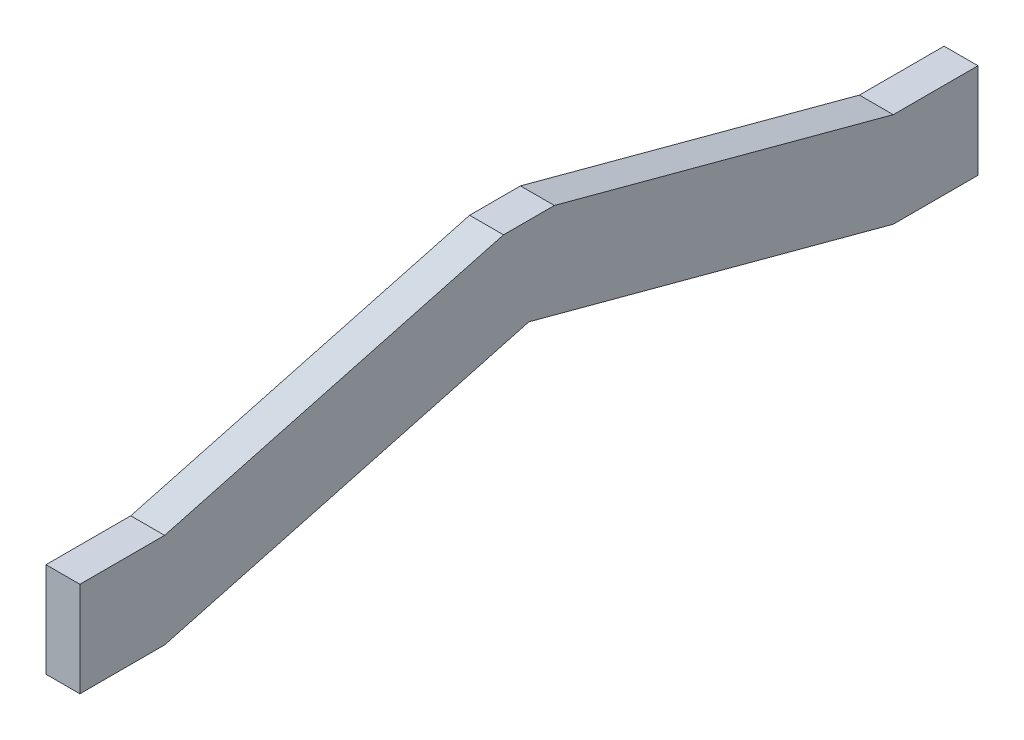
SolidWorks part; units mm, degrees
ref_plane "Front Plane" through (0, 0, 0) normal (0, 0, 1) x (1, 0, 0)
ref_plane "Top Plane" through (0, 0, 0) normal (0, 1, 0) x (1, 0, 0)
ref_plane "Right Plane" through (0, 0, 0) normal (1, 0, 0) x (0, 0, -1)
sketch "Sketch1" plane through (0, 0, 0) normal (1, 0, 0) x (0, 0, -1)
  line L10 (0, 0) -> (-25, 0)
  line L11 (-25, 0) -> (-132.5, 28.8045)
  line L12 (-132.5, 28.8045) -> (-240, 0)
  line L13 (-240, 0) -> (-265, 0)
  line L14 (-265, 0) -> (-265, 28)
  line L15 (-265, 28) -> (-240, 28)
  line L16 (-240, 28) -> (-140, 54.7949)
  line L17 (-140, 54.7949) -> (-125, 54.7949)
  line L18 (-125, 54.7949) -> (-25, 28)
  line L19 (-25, 28) -> (0, 28)
  line L20 (0, 28) -> (0, 0)
  line L21 (-132.5, 28.8045) -> (-132.5, 54.7949) construction
  point P10 (-132.5, 54.7949)
  dimension "D1" = 15
  dimension "D2" = 28
  dimension "D3" = 15
  dimension "D4" = 25
  dimension "D5" = 265
  dimension "D6" = 25
extrude "Boss-Extrude1" add sketch "Sketch1" along normal blind 10
